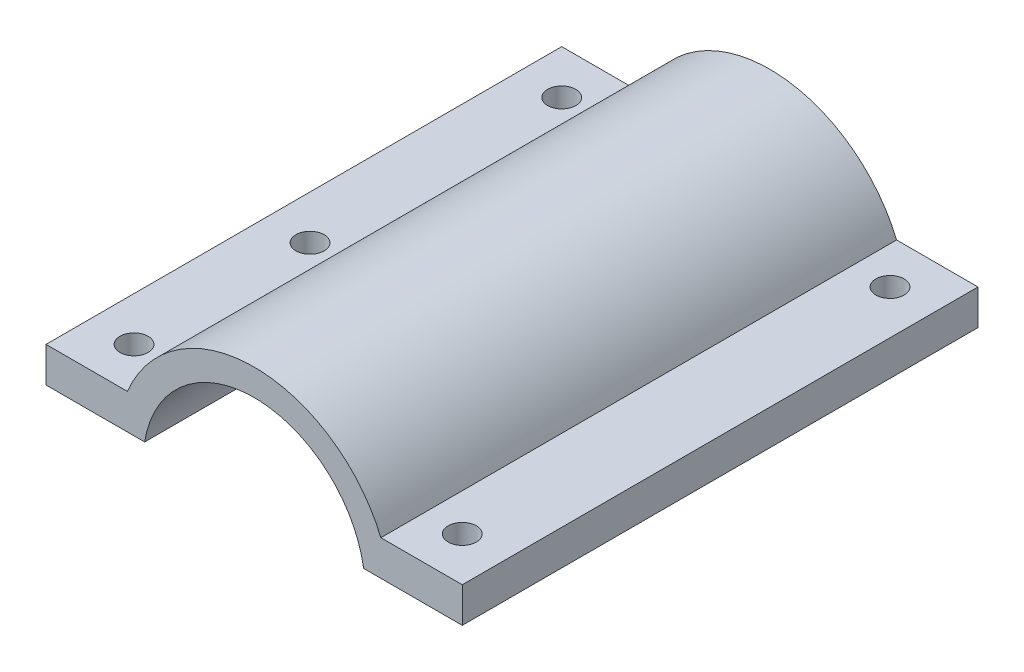
SolidWorks part; units mm, degrees
ref_plane "Front Plane" through (0, 0, 0) normal (0, 0, 1) x (1, 0, 0)
ref_plane "Top Plane" through (0, 0, 0) normal (0, 1, 0) x (1, 0, 0)
ref_plane "Right Plane" through (0, 0, 0) normal (1, 0, 0) x (0, 0, -1)
sketch "Sketch1" plane through (0, 0, 0) normal (0, 0, 1) x (1, 0, 0)
  line L0 (-23.65, 6) -> (-14.4, 6)
  line L1 (14.4, 6) -> (23.65, 6)
  line L2 (-23.65, 6) -> (-23.65, 2)
  line L3 (-23.65, 2) -> (-12.4403, 2)
  line L4 (23.65, 6) -> (23.65, 2)
  line L5 (23.65, 2) -> (12.4403, 2)
  arc A0 (12.4403, 2) -> (-12.4403, 2) centre (0, 0) ccw
  arc A2 (14.4, 6) -> (-14.4, 6) centre (0, 0) ccw
  point P6 (-15.4713, 2)
  point P12 (-12.4403, 2)
  point P13 (12.4403, 2)
  dimension "D1" = 25.2
  dimension "D2" = 3
  dimension "D3" = 47.3
  dimension "D4" = 6
  dimension "D5" = 4
  dimension "D6" = 4
  dimension "D7" = 23.65
extrude "Boss-Extrude1" add sketch "Sketch1" along normal blind 58.6
sketch "Sketch2" plane through (0, 6, 0) normal (0, 1, 0) x (1, 0, 0)
  line L0 (23.65, -58.6) -> (23.65, 0) construction
  line L1 (23.65, -58.6) -> (14.4, -58.6) construction
  line L2 (23.65, 0) -> (14.4, 0) construction
  line L3 (-23.65, -58.6) -> (-23.65, 0) construction
  line L4 (-14.4, -58.6) -> (-23.65, -58.6) construction
  line L5 (-14.4, 0) -> (-23.65, 0) construction
  circle A0 centre (18.65, -5) radius 1.6
  circle A1 centre (18.65, -53.6) radius 1.6
  circle A2 centre (-18.65, -53.6) radius 1.6
  circle A3 centre (-18.65, -5) radius 1.6
  circle A4 centre (-18.65, -33.6) radius 1.6
  dimension "D1" = 3.2
  dimension "D2" = 3.2
  dimension "D3" = 3.2
  dimension "D4" = 3.2
  dimension "D5" = 3.2
  dimension "D6" = 5
  dimension "D7" = 5
  dimension "D8" = 5
  dimension "D9" = 5
  dimension "D10" = 5
  dimension "D11" = 5
  dimension "D12" = 5
  dimension "D13" = 5
  dimension "D14" = 5
  dimension "D15" = 25
extrude "Cut-Extrude1" cut sketch "Sketch2" against normal blind 58.6
